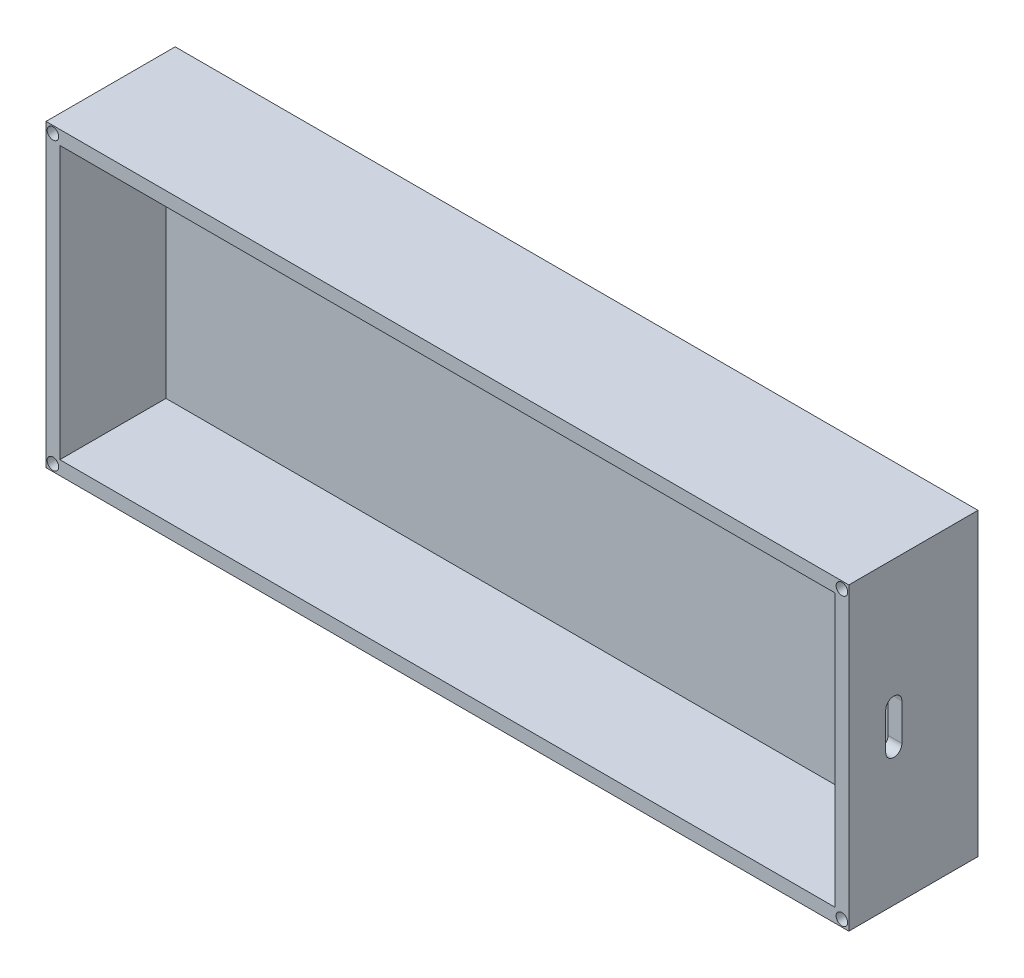
SolidWorks part; units mm, degrees
ref_plane "Front Plane" through (0, 0, 0) normal (0, 0, 1) x (1, 0, 0)
ref_plane "Top Plane" through (0, 0, 0) normal (0, 1, 0) x (1, 0, 0)
ref_plane "Right Plane" through (0, 0, 0) normal (1, 0, 0) x (0, 0, -1)
sketch "Sketch1" plane through (0, 0, 0) normal (0, 0, 1) x (1, 0, 0)
  line L1 (87, -32.5) -> (-87, -32.5)
  line L2 (87, -32.5) -> (87, 32.5)
  line L3 (87, 32.5) -> (-87, 32.5)
  line L4 (-87, -32.5) -> (-87, 32.5)
  line L5 (87, -32.5) -> (-87, 32.5) construction
  line L6 (87, 32.5) -> (-87, -32.5) construction
  point P0 (0, 0)
  dimension "D1" = 65
  dimension "D2" = 174
extrude "Boss-Extrude1" add sketch "Sketch1" along normal blind 5
sketch "Sketch3" plane through (0, 0, 5) normal (0, 0, 1) x (1, 0, 0)
  line L1 (-87, 32.5) -> (87, 32.5)
  line L2 (-87, 32.5) -> (-87, -32.5)
  line L3 (-87, -32.5) -> (87, -32.5)
  line L4 (87, 32.5) -> (87, -32.5)
  line L5 (-87, 32.5) -> (87, 32.5)
  line L6 (-87, 32.5) -> (-87, -32.5)
  line L7 (-87, -32.5) -> (87, -32.5)
  line L8 (87, 32.5) -> (87, -32.5)
  line L16 (-84, 29.5) -> (-84, -29.5)
  line L17 (-84, -29.5) -> (84, -29.5)
  line L18 (84, -29.5) -> (84, 29.5)
  line L19 (84, 29.5) -> (-84, 29.5)
  line L20 (-84, 29.5) -> (-84, -29.5)
  line L21 (-84, -29.5) -> (84, -29.5)
  line L22 (84, -29.5) -> (84, 29.5)
  line L23 (84, 29.5) -> (-84, 29.5)
  line M7 (-87, 32.5) -> (-87, -32.5)
  line M8 (-87, -32.5) -> (87, -32.5)
  line M9 (87, -32.5) -> (87, 32.5)
  line M10 (87, 32.5) -> (-87, 32.5)
  dimension "D1" = 3
extrude "Boss-Extrude3" add sketch "Sketch3" along normal blind 23 contours L23 L22 L21 L20 M10 M7 M8 M9
sketch "Sketch9" plane through (87, 0, 0) normal (1, 0, 0) x (0, 0, -1)
  line L0 (-18.25, -3) -> (-18.25, 5) construction
  line L1 (-20, -3) -> (-20, 5)
  line L2 (-16.5, -3) -> (-16.5, 5)
  line L3 (-28, -32.5) -> (0, -32.5) construction
  line L4 (0, -32.5) -> (0, 32.5) construction
  arc A0 (-20, -3) -> (-16.5, -3) centre (-18.25, -3) ccw
  arc A1 (-16.5, 5) -> (-20, 5) centre (-18.25, 5) ccw
  point P2 (-18.25, 1)
  dimension "D1" = 8
  dimension "D2" = 3.5
  dimension "D3" = 29.5
  dimension "16.50" = 16.5
extrude "Cut-Extrude1" cut sketch "Sketch9" against normal blind 23
sketch "Sketch17" plane through (0, 0, 28) normal (0, 0, 1) x (1, 0, 0)
  line L0 (-84, 29.5) -> (-87, 32.5) construction
  line L1 (-87, -32.5) -> (-84, -29.5) construction
  line L2 (87, 32.5) -> (84, 29.5) construction
  line L3 (84, -29.5) -> (87, -32.5) construction
  circle A0 centre (-85.5, -31) radius 1.25
  circle A1 centre (-85.5, 31) radius 1.25
  circle A2 centre (85.5, 31) radius 1.25
  circle A3 centre (85.5, -31) radius 1.25
  dimension "D1" = 2.5
  dimension "D2" = 2.5
  dimension "D3" = 2.5
  dimension "D4" = 2.5
extrude "Cut-Extrude5" cut sketch "Sketch17" against normal blind 4
sketch "Sketch15" plane through (0, 0, 28) normal (0, 0, 1) x (1, 0, 0)
  line L0 (-87, 32.5) -> (-84, 29.5) construction
  circle A0 centre (-85.5, 31) radius 1.25
  dimension "D1" = 2.5
extrude "Cut-Extrude4" cut sketch "Sketch15" against normal blind 4
sketch "Sketch11" plane through (0, 0, 28) normal (0, 0, 1) x (1, 0, 0)
  line L0 (-87, 32.5) -> (-84, 29.5) construction
  circle A0 centre (-85.5, 31) radius 0.0844
  circle A1 centre (-85.5, 31) radius 1.25
  dimension "D1" = 2.5
extrude "Cut-Extrude2" cut sketch "Sketch11" against normal blind 4
sketch "Sketch13" plane through (0, 0, 28) normal (0, 0, 1) x (1, 0, 0)
  circle A0 centre (-85.5, 31) radius 0.0844
extrude "Cut-Extrude3" cut sketch "Sketch13" against normal blind 4
